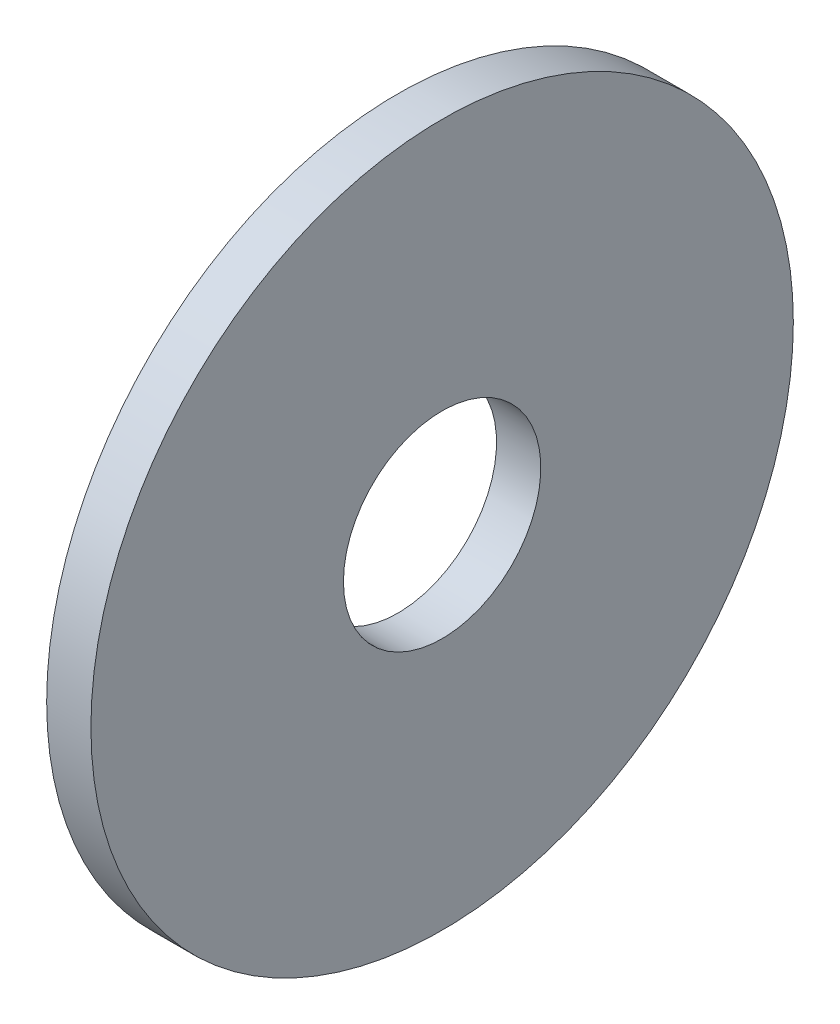
SolidWorks part; units mm, degrees
ref_plane "Plane1" through (0, 0, 0) normal (0, 0, 1) x (1, 0, 0)
ref_plane "Plane2" through (0, 0, 0) normal (0, 1, 0) x (1, 0, 0)
ref_plane "Plane3" through (0, 0, 0) normal (1, 0, 0) x (0, 0, -1)
sketch "Sketch1" plane through (0, 0, 0) normal (0, 0, 1) x (1, 0, 0)
  line L0 (-34.925, 0) -> (9.525, 0) construction
  line L1 (0, 3.5687) -> (0, 12.7)
  line L2 (0, 12.7) -> (-1.6002, 12.7)
  line L3 (-1.6002, 12.7) -> (-1.6002, 3.5687)
  line L4 (-1.6002, 3.5687) -> (0, 3.5687)
  dimension "Thickness" = 1.6002
  dimension "Inside_dia" = 7.1374
  dimension "Outside_dia" = 25.4
revolve "Base-Revolve" add sketch "Sketch1" angle 360 about L0
